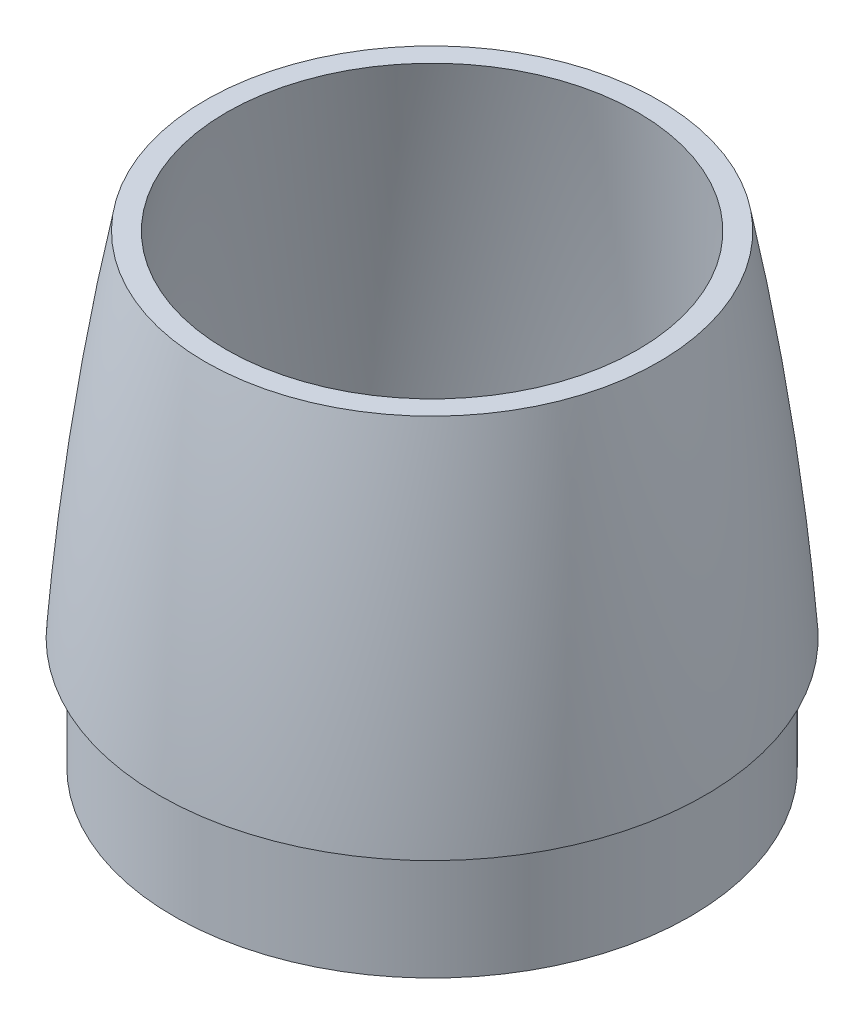
SolidWorks part; units mm, degrees
material "PVB"
ref_plane "Front Plane" through (0, 0, 0) normal (0, 0, 1) x (1, 0, 0)
ref_plane "Top Plane" through (0, 0, 0) normal (0, 1, 0) x (1, 0, 0)
ref_plane "Right Plane" through (0, 0, 0) normal (1, 0, 0) x (0, 0, -1)
sketch "Sketch2" plane through (0, 0, 0) normal (0, 0, 1) x (1, 0, 0)
  line L0 (0, 0) -> (0, 381) construction
  line L1 (-98.425, 0) -> (-90.551, 0)
  line L2 (0, 381) -> (0, 375.92)
  arc A0 (0, 381) -> (-98.425, 0) centre (992.1135, -78.5092) ccw
  arc A1 (0, 375.92) -> (-90.551, 0) centre (1112.691, -90.9691) ccw
  dimension "D1" = 381
  dimension "D2" = 5.08
  dimension "D3" = 98.425
  dimension "D4" = 7.874
revolve "Revolve1" add sketch "Sketch2" angle 360 about L2
sketch "Sketch3" plane through (0, 0, 0) normal (0, -1, 0) x (1, 0, 0)
  circle A0 centre (0, 0) radius 88.9
  circle A1 centre (0, 0) radius 86.995
  dimension "D1" = 177.8
extrude "Boss-Extrude1" [suppressed] add sketch "Sketch3" along normal blind 35.56
sketch "Sketch4" plane through (0, 0, 0) normal (0, -1, 0) x (-1, 0, 0)
  circle A0 centre (0, 0) radius 93.1545
  circle A1 centre (0, 0) radius 90.4875
  dimension "D1" = 186.309
  dimension "D2" = 180.975
extrude "Boss-Extrude2" add sketch "Sketch4" along normal blind 40.4
ref_plane "Plane1" through (0, -17.54, 0) normal (0, -1, 0) x (-1, 0, 0)
sketch "Sketch6" plane through (0, -17.54, 0) normal (0, -1, 0) x (-1, 0, 0)
  circle A0 centre (0, 0) radius 221.0288
extrude "Cut-Extrude1" [suppressed] cut sketch "Sketch6" against normal blind 457.2
ref_plane "Plane2" through (0, 381, 0) normal (0, 1, 0) x (1, 0, 0)
sketch "Sketch7" plane through (0, 381, 0) normal (0, 1, 0) x (1, 0, 0)
  circle A0 centre (0, 0) radius 317.5
  dimension "D1" = 635
extrude "Cut-Extrude2" cut sketch "Sketch7" against normal blind 254
